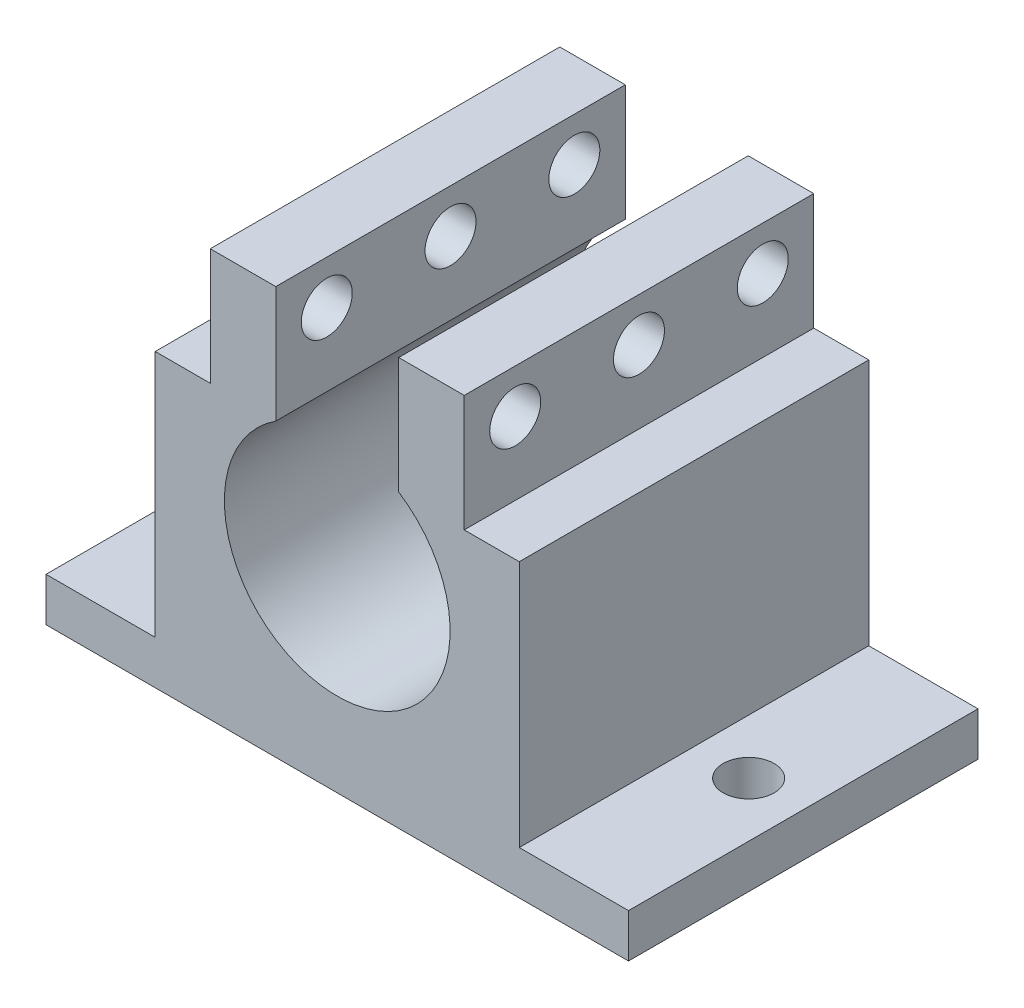
SolidWorks part; units mm, degrees
ref_plane "Alzado" through (0, 0, 0) normal (0, 0, 1) x (1, 0, 0)
ref_plane "Planta" through (0, 0, 0) normal (0, 1, 0) x (1, 0, 0)
ref_plane "Vista lateral" through (0, 0, 0) normal (1, 0, 0) x (0, 0, -1)
sketch "Croquis1" plane through (0, 0, 0) normal (0, 0, 1) x (1, 0, 0)
  line L0 (-4.2205, 10) -> (-12.5, 10)
  line L1 (12.5, -10) -> (-12.5, -10)
  line L2 (12.5, -10) -> (12.5, 10)
  line L3 (12.5, 10) -> (4.2205, 10)
  line L4 (-12.5, -10) -> (-12.5, 10)
  line L5 (12.5, -10) -> (-12.5, 10) construction
  line L6 (12.5, 10) -> (-12.5, -10) construction
  arc A0 (-4.2205, 10) -> (4.2205, 10) centre (0, 3.5) ccw
  point P0 (0, 0)
  dimension "D3" = 15.5
  dimension "D4" = 3.5
  dimension "D1" = 20
  dimension "D2" = 25
extrude "Saliente-Extruir2" add sketch "Croquis1" along normal blind 24
sketch "Croquis2" plane through (0, 0, 0) normal (0, 0, 1) x (1, 0, 0)
  line L1 (-4.2205, 10) -> (-8.7205, 10)
  line L2 (-4.2205, 10) -> (-4.2205, 18)
  line L3 (-4.2205, 18) -> (-8.7205, 18)
  line L4 (-8.7205, 10) -> (-8.7205, 18)
  line L5 (4.2205, 10) -> (8.7205, 10)
  line L6 (4.2205, 10) -> (4.2205, 18)
  line L7 (4.2205, 18) -> (8.7205, 18)
  line L8 (8.7205, 10) -> (8.7205, 18)
  dimension "D1" = 4.5
  dimension "D2" = 8
  dimension "D3" = 4.5
  dimension "D4" = 8
extrude "Saliente-Extruir3" add sketch "Croquis2" along normal up to surface (24 mm away) up to face at (0, 0.9583, 24)
sketch "Croquis3" plane through (0, 0, 0) normal (0, 0, 1) x (1, 0, 0)
  line L1 (-12.5, -10) -> (-20, -10)
  line L2 (-12.5, -10) -> (-12.5, -7)
  line L3 (-12.5, -7) -> (-20, -7)
  line L4 (-20, -10) -> (-20, -7)
  line L5 (12.5, -10) -> (20, -10)
  line L6 (12.5, -10) -> (12.5, -7)
  line L7 (12.5, -7) -> (20, -7)
  line L8 (20, -10) -> (20, -7)
  dimension "D1" = 3
  dimension "D2" = 3
extrude "Saliente-Extruir4" add sketch "Croquis3" along normal up to surface (24 mm away) up to face at (0, 8.1458, 24)
sketch "Croquis4" plane through (0, 0, 0) normal (1, 0, 0) x (0, 0, -1)
  line L0 (-24, 18) -> (0, 18) construction
  line L1 (-24, 10) -> (-24, 18) construction
  line L2 (0, 10) -> (0, 18) construction
  circle A0 centre (-20.5, 15) radius 1.75
  circle A1 centre (-12, 15) radius 1.75
  circle A2 centre (-3.5, 15) radius 1.75
  point P8 (-12, 18)
  dimension "D1" = 3.5
  dimension "D2" = 3.5
  dimension "D3" = 3.5
  dimension "D4" = 0
  dimension "D5" = 3.5
  dimension "D6" = 3.5
  dimension "D7" = 3
  dimension "D8" = 3
  dimension "D9" = 3
extrude "Cortar-Extruir1" cut sketch "Croquis4" along normal up to surface (17.441 mm away) from surface at -8.7205 up to face at (8.7205, 14, 12) starting at face at (-8.7205, 14, 12)
sketch "Croquis5" plane through (0, 0, 0) normal (0, 1, 0) x (1, 0, 0)
  line L0 (-20, -24) -> (-20, 0) construction
  line L1 (20, -24) -> (20, 0) construction
  line L2 (-12.5, 0) -> (-20, 0) construction
  line L3 (20, 0) -> (12.5, 0) construction
  circle A0 centre (-16.25, -12) radius 1.75
  circle A1 centre (16.25, -12) radius 1.75
  point P9 (-20, -12)
  point P10 (20, -12)
  point P14 (-16.25, 0)
  point P17 (16.25, 0)
  dimension "D3" = 3.5
  dimension "D4" = 3.5
  dimension "D1" = 0
  dimension "D2" = 0
  dimension "D5" = 0
  dimension "D6" = 0
extrude "Cortar-Extruir2" cut sketch "Croquis5" against normal up to surface (10 mm away) up to face at (0, -10, 12)
